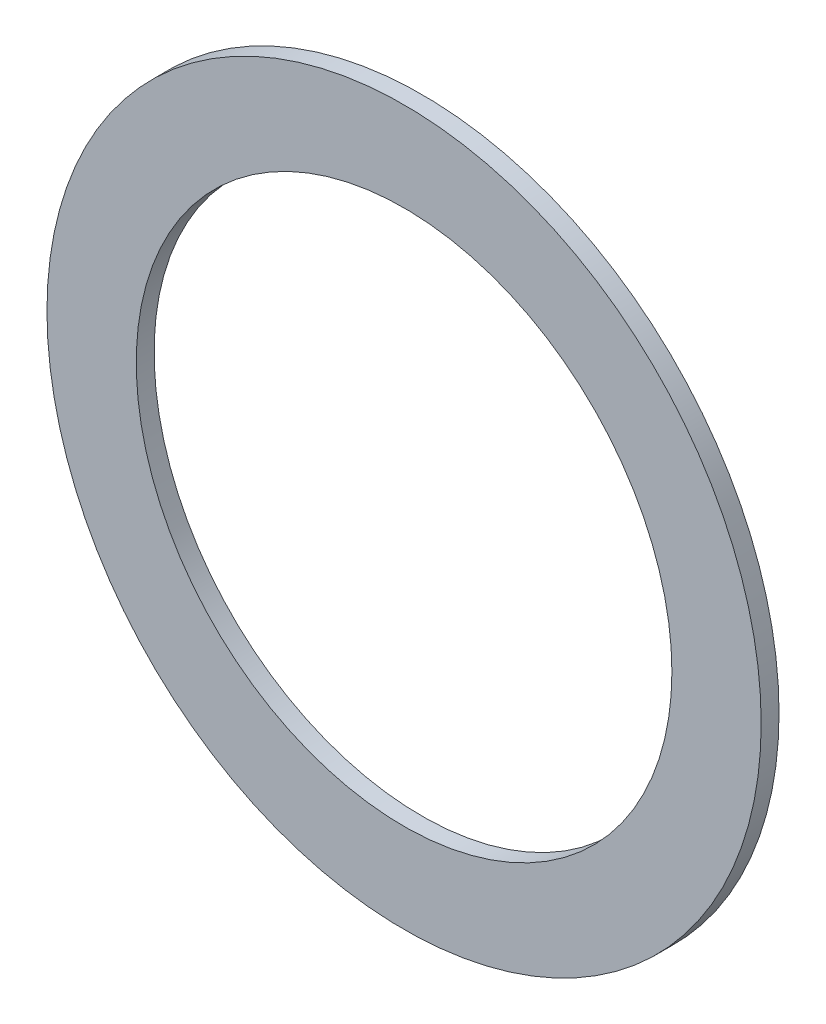
SolidWorks part; units mm, degrees
ref_plane "Front Plane" through (0, 0, 0) normal (0, 0, 1) x (1, 0, 0)
ref_plane "Top Plane" through (0, 0, 0) normal (0, 1, 0) x (1, 0, 0)
ref_plane "Right Plane" through (0, 0, 0) normal (1, 0, 0) x (0, 0, -1)
sketch "Sketch1" plane through (0, 0, 0) normal (0, 0, 1) x (1, 0, 0)
  circle A0 centre (0, 0) radius 100
  dimension "D1" = 200
extrude "Boss-Extrude1" add sketch "Sketch1" along normal blind 5
sketch "Sketch2" plane through (0, 0, 5) normal (0, 0, 1) x (1, 0, 0)
  circle A0 centre (0, 0) radius 75
  dimension "D1" = 150
extrude "Cut-Extrude1" cut sketch "Sketch2" against normal through all
sketch "Sketch3" plane through (0, 0, 0) normal (0, 0, 1) x (1, 0, 0)
  line L0 (4.3301, -2.5) -> (67.0086, 33.6874)
  line L1 (0, 0) -> (-64.9519, 37.5) construction
  line L2 (0, 5) -> (62.6785, 41.1874)
  line L3 (0, 0) -> (0, 5) construction
  line L4 (0, 5) -> (4.3301, -2.5) construction
  line L5 (0, 5) -> (-4.3301, -2.5) construction
  line L6 (4.3301, -2.5) -> (-4.3301, -2.5) construction
  line L7 (0, 5) -> (-62.6785, 41.1874)
  line L8 (-4.3301, -2.5) -> (-67.0086, 33.6874)
  line L9 (-4.3301, -2.5) -> (-4.3301, -74.8749)
  line L10 (4.3301, -2.5) -> (4.3301, -74.8749)
  circle A0 centre (0, 0) radius 5 construction
  circle A2 centre (0, 0) radius 75 construction
  point P3 (0, 0)
  point P22 (0, 0)
  dimension "D1" = 3
  dimension "D3" = 10
  dimension "D2" = 60
  dimension "D4" = 60
